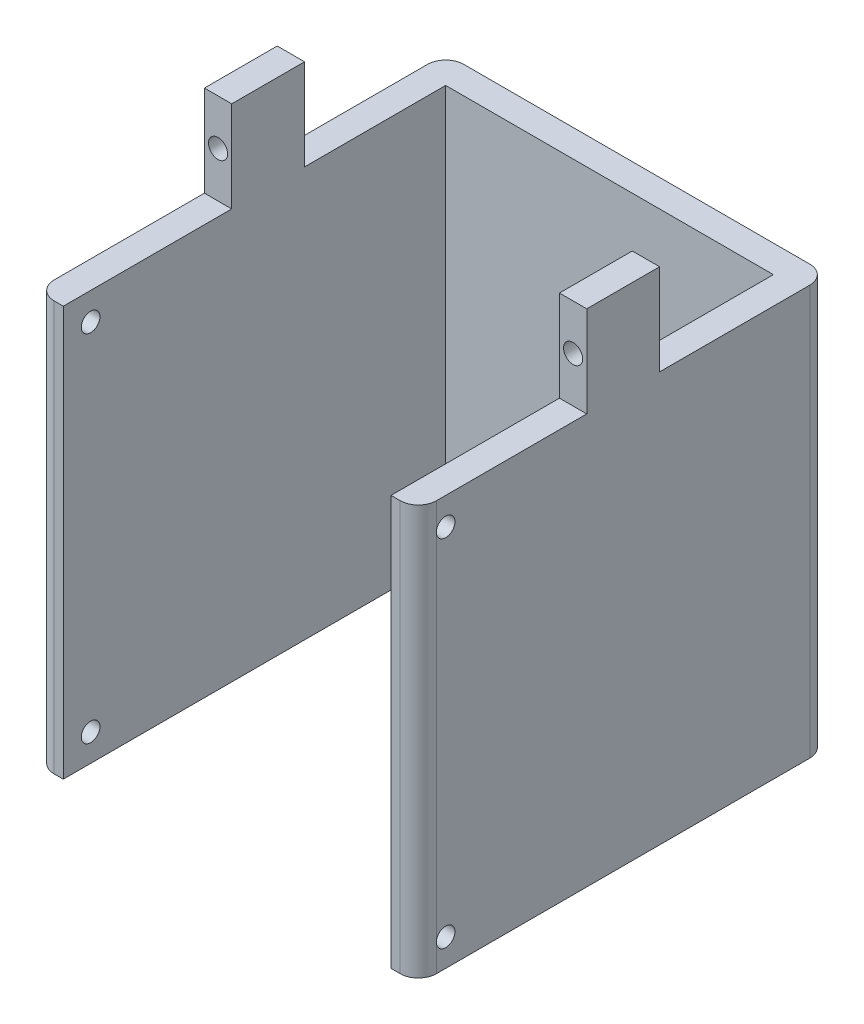
SolidWorks part; units mm, degrees
ref_plane "前基準面" through (0, 0, 0) normal (0, 0, 1) x (1, 0, 0)
ref_plane "上基準面" through (0, 0, 0) normal (0, 1, 0) x (1, 0, 0)
ref_plane "右基準面" through (0, 0, 0) normal (1, 0, 0) x (0, 0, -1)
sketch "草圖1" plane through (0, 0, 0) normal (0, 0, 1) x (1, 0, 0)
  line L0 (-14.5455, -28.0909) -> (-15.5455, -28.0909)
  line L1 (-14.5455, 16.9091) -> (25.4545, 16.9091)
  line L3 (-14.5455, -28.0909) -> (25.4545, -28.0909)
  line L5 (-15.5455, -28.0909) -> (-15.5455, 16.9091)
  line L6 (-15.5455, 16.9091) -> (-14.5455, 16.9091)
  line L8 (26.4545, -28.0909) -> (26.4545, 16.9091)
  line L9 (26.4545, 16.9091) -> (25.4545, 16.9091)
  line L10 (26.4545, -28.0909) -> (25.4545, -28.0909)
  dimension "D1" = 40
  dimension "D2" = 45
  dimension "D3" = 1
  dimension "D4" = 1
extrude "填料-伸長1" add sketch "草圖1" along normal blind 40 and the other way blind 5 contours L3 L10 L8 L9 L1 L6 L5 L0
sketch "草圖2" plane through (0, 16.9091, 0) normal (0, 1, 0) x (1, 0, 0)
  line L0 (5.4545, 5) -> (5.4545, -40.6532) construction
  line L1 (-15.5455, 5) -> (26.4545, 5) construction
  line L2 (-15.5455, -40) -> (26.4545, -40) construction
  line L3 (-12.5455, -3) -> (23.4545, -3)
  line L4 (-12.5455, -3) -> (-12.5455, -40)
  line L5 (-12.5455, -40) -> (23.4545, -40)
  line L6 (23.4545, -3) -> (23.4545, -40)
  dimension "D3" = 37
extrude "除料-伸長1" cut sketch "草圖2" against normal blind 50
sketch "草圖5" plane through (0, 16.9091, 0) normal (0, 1, 0) x (1, 0, 0)
  line L1 (-12.5455, -3) -> (23.4545, -3)
  line L2 (-12.5455, -3) -> (-12.5455, 2)
  line L3 (-12.5455, 2) -> (23.4545, 2)
  line L4 (23.4545, -3) -> (23.4545, 2)
  dimension "D1" = 36
  dimension "D2" = 5
extrude "除料-伸長4" cut sketch "草圖5" against normal blind 43
ref_plane "平面1" through (0, 16.9091, 0) normal (0, 1, 0) x (1, 0, 0)
ref_plane "平面2" through (0, -28.0909, 0) normal (0, -1, 0) x (-1, 0, 0)
ref_plane "平面4" through (-15.5455, 0, 0) normal (-1, 0, 0) x (0, 0, 1)
sketch "草圖9" plane through (-15.5455, 0, 0) normal (-1, 0, 0) x (0, 0, 1)
  line L3 (-5, -28.0909) -> (40, -28.0909) construction
  line L4 (40, -28.0909) -> (40, 16.9091) construction
  line L5 (-5, 16.9091) -> (40, 16.9091) construction
  circle A2 centre (37, -25.0909) radius 1.025
  circle A3 centre (37, 13.9091) radius 1.025
  dimension "D1" = 2.05
  dimension "D2" = 2.05
  dimension "D3" = 3
  dimension "D4" = 3
  dimension "D5" = 3
  dimension "D6" = 3
extrude "除料-伸長5" cut sketch "草圖9" against normal blind 45.5
sketch "草圖10" plane through (0, 16.9091, 0) normal (0, 1, 0) x (1, 0, 0)
  line L0 (5.4545, -3) -> (5.4545, 10.5844) construction
  line L1 (-12.5455, -3) -> (23.4545, -3) construction
  line L5 (-15.5455, -17.5) -> (26.4545, -17.5) construction
  line L6 (-15.5455, 24.75) -> (-15.5455, -24.75) construction
  line L7 (26.4545, 5) -> (26.4545, -40) construction
  line L8 (-15.5455, 5) -> (26.4545, 5) construction
  line L10 (-12.5455, 2) -> (-12.5455, -40) construction
  line L11 (-15.5455, -13.5) -> (-12.5455, -13.5)
  line L12 (-15.5455, -13.5) -> (-15.5455, -21.5)
  line L13 (-15.5455, -21.5) -> (-12.5455, -21.5)
  line L14 (-12.5455, -13.5) -> (-12.5455, -21.5)
  line L15 (26.4545, -21.5) -> (23.4545, -21.5)
  line L16 (23.4545, -13.5) -> (23.4545, -21.5)
  line L17 (26.4545, -13.5) -> (23.4545, -13.5)
  line L18 (26.4545, -13.5) -> (26.4545, -21.5)
  dimension "D1" = 22.5
  dimension "D2" = 4
  dimension "D3" = 3
  dimension "D4" = 4
extrude "填料-伸長4" add sketch "草圖10" along normal blind 10
sketch "草圖11" plane through (0, -28.0909, 0) normal (0, -1, 0) x (-1, 0, 0)
  line L0 (-26.4545, -17.5) -> (15.8441, -17.5) construction
  line L1 (-26.4545, 5) -> (-26.4545, -40) construction
  line L2 (-26.4545, 5) -> (15.5455, 5) construction
  line L3 (-5.4545, 5) -> (-5.4545, -41.7705) construction
  line L4 (-26.4545, -40) -> (-23.4545, -40)
  line L5 (-26.4545, -13.5) -> (-23.4545, -13.5)
  line L6 (-26.4545, -13.5) -> (-26.4545, 5)
  line L7 (-26.4545, 5) -> (-23.4545, 5)
  line L8 (-23.4545, -13.5) -> (-23.4545, 5)
  line L9 (-23.4545, -21.5) -> (-23.4545, -40)
  line L10 (-26.4545, -21.5) -> (-23.4545, -21.5)
  line L11 (-26.4545, -21.5) -> (-26.4545, -40)
  line L12 (15.5455, -21.5) -> (15.5455, -40)
  line L13 (15.5455, -21.5) -> (12.5455, -21.5)
  line L14 (12.5455, -21.5) -> (12.5455, -40)
  line L15 (15.5455, -40) -> (12.5455, -40)
  line L16 (15.5455, 5) -> (12.5455, 5)
  line L17 (12.5455, -13.5) -> (12.5455, 5)
  line L18 (15.5455, -13.5) -> (12.5455, -13.5)
  line L19 (15.5455, -13.5) -> (15.5455, 5)
  dimension "D1" = 22.5
  dimension "D2" = 21
  dimension "D3" = 3
  dimension "D4" = 4
ref_plane "平面5" through (0, 0, 13.5) normal (0, 0, -1) x (-1, 0, 0)
sketch "草圖12" plane through (0, 0, 13.5) normal (0, 0, -1) x (-1, 0, 0)
  line L0 (-24.9545, 26.9091) -> (-24.9545, 15.9652) construction
  line L1 (-26.4545, 26.9091) -> (-23.4545, 26.9091) construction
  line L2 (-26.4545, 21.9091) -> (15.5455, 21.9091) construction
  line L3 (-26.4545, 26.9091) -> (-26.4545, 16.9091) construction
  line L4 (15.5455, -24.75) -> (15.5455, 24.75) construction
  line L5 (-5.4545, 21.9091) -> (-5.4545, -4.7924) construction
  circle A0 centre (-24.9545, 21.9091) radius 1.05
  circle A1 centre (14.0455, 21.9091) radius 1.05
  dimension "D1" = 2.1
  dimension "D2" = 2.1
extrude "除料-伸長6" cut sketch "草圖12" against normal blind 10
ref_plane "平面6" through (0, 0, -5) normal (0, 0, -1) x (-1, 0, 0)
fillet "圓角4" radius 2 1 edges at (26.4545, -5.5909, -5)
fillet "圓角5" radius 2 1 edges at (-15.5455, -5.5909, -5)
fillet "圓角6" radius 2 1 edges at (26.4545, -5.5909, 40)
fillet "圓角7" radius 2 1 edges at (-15.5455, -5.5909, 40)
